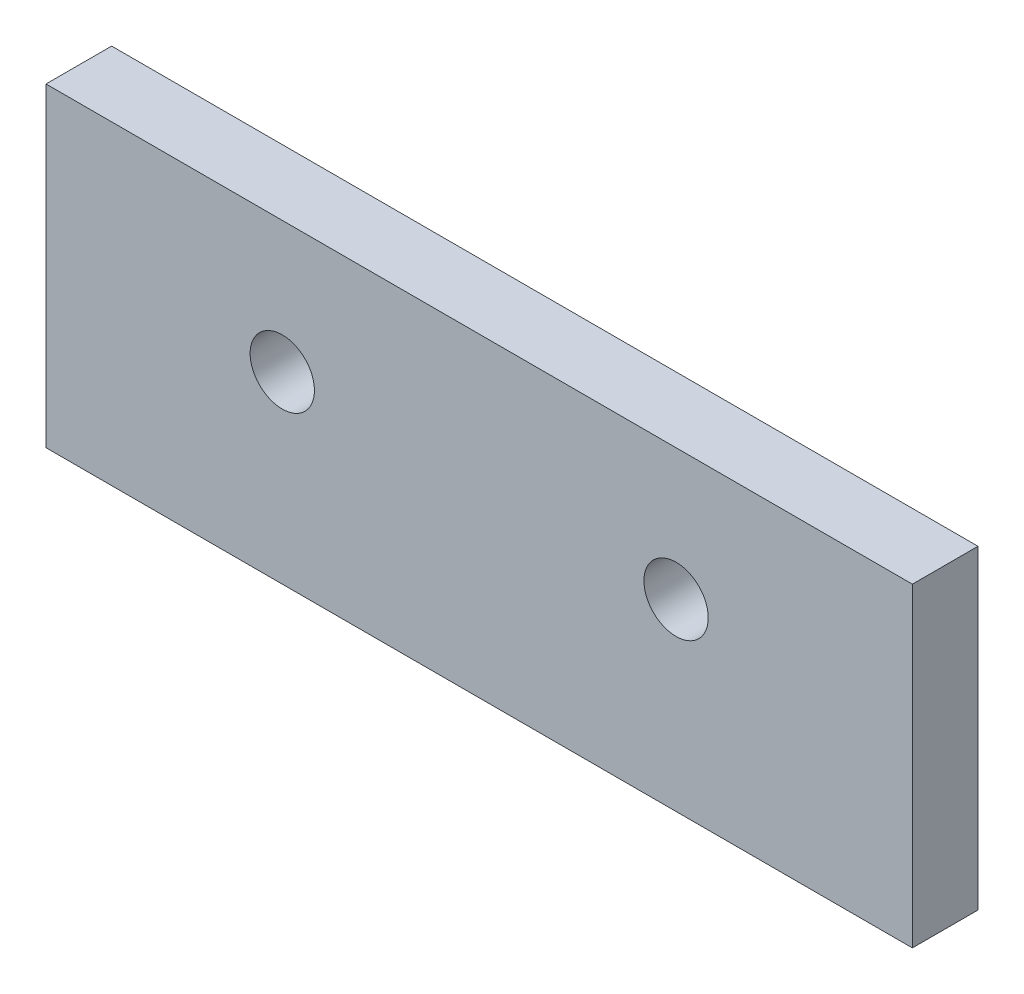
SolidWorks part; units mm, degrees
ref_plane "Front Plane" through (0, 0, 0) normal (0, 0, 1) x (1, 0, 0)
ref_plane "Top Plane" through (0, 0, 0) normal (0, 1, 0) x (1, 0, 0)
ref_plane "Right Plane" through (0, 0, 0) normal (1, 0, 0) x (0, 0, -1)
sketch "Sketch2" plane through (0, 0, 0) normal (0, 0, 1) x (1, 0, 0)
  line L5 (-22.4835, 0) -> (43.5165, 0)
  line L6 (-22.4835, 0) -> (-22.4835, -24)
  line L7 (-22.4835, -24) -> (43.5165, -24)
  line L8 (43.5165, 0) -> (43.5165, -24)
  circle A0 centre (-4.4835, -10) radius 2.45
  circle A1 centre (25.5165, -10) radius 2.45
  dimension "D7" = 4.9
  dimension "D8" = 4.9
  dimension "D1" = 66
  dimension "D2" = 24
  dimension "D3" = 18
  dimension "D4" = 14
  dimension "D5" = 18
  dimension "D6" = 14
extrude "Boss-Extrude1" add sketch "Sketch2" along normal blind 5
